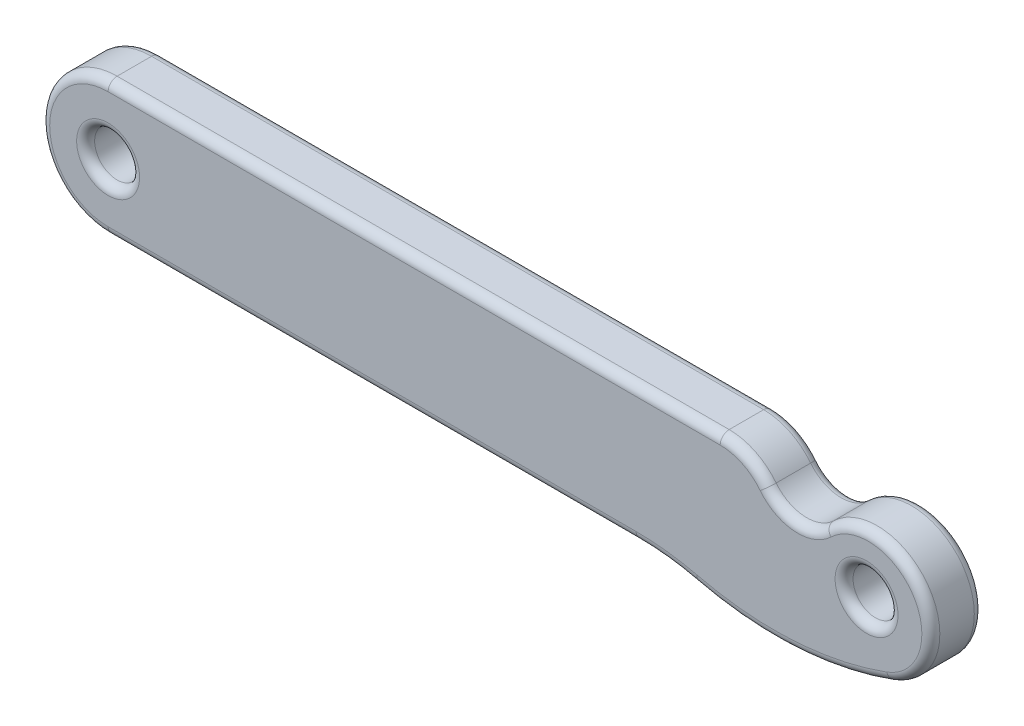
SolidWorks part; units mm, degrees
ref_plane "Front" through (0, 0, 0) normal (0, 0, 1) x (1, 0, 0)
ref_plane "Top" through (0, 0, 0) normal (0, 1, 0) x (1, 0, 0)
ref_plane "Right" through (0, 0, 0) normal (1, 0, 0) x (0, 0, -1)
sketch "Sketch1" plane through (0, 0, 0) normal (0, 0, 1) x (1, 0, 0)
  line L0 (0, 0) -> (25.3139, 0) construction
  line L1 (0, 2.25) -> (25.3139, 2.25)
  line L2 (0, -2.25) -> (25.3139, -2.25)
  circle A0 centre (0, 0) radius 0.75
  arc A1 (0, 2.25) -> (0, -2.25) centre (0, 0) ccw
  arc A2 (25.3139, -2.25) -> (25.3139, 2.25) centre (25.3139, 0) ccw
  circle A3 centre (25.3139, 0) radius 0.75
  point P3 (12.657, 0)
  dimension "D1" = 1.5
  dimension "D2" = 25.3139
  dimension "D3" = 1.5
extrude "Boss-Extrude1" add sketch "Sketch1" along normal blind 1.75
sketch "Sketch2" plane through (0, 0, 0) normal (0, 0, 1) x (1, 0, 0)
  circle A1 centre (23.0178, 2.2961) radius 1
  point P1 (20.5222, 2.2705)
sketch "Sketch3" plane through (0, 0, 1.75) normal (0, 0, 1) x (1, 0, 0)
  line L1 (20.4287, 2.25) -> (19.3427, 2.25)
  line L3 (25.3139, 2.25) -> (0, 2.25) construction
  line L6 (25.0484, -2.2343) -> (28.6572, -4.175)
  line L7 (28.6572, -4.175) -> (32.3716, 3.4229)
  line L8 (32.3716, 3.4229) -> (23.3874, 7.4223)
  line L9 (23.3874, 7.4223) -> (19.3427, 2.25)
  arc A2 (20.4287, 2.25) -> (21.9979, 1.4901) centre (20.4287, 0.25) cw
  arc A10 (25.0484, -2.2343) -> (26.0877, -2.1128) centre (25.3139, 0) ccw
  arc A11 (25.3139, -2.25) -> (25.3139, 2.25) centre (25.3139, 0) ccw construction
  arc A12 (21.9979, 1.4901) -> (23.9188, 1.359) centre (23.0178, 2.2961) ccw
  circle A13 centre (23.0178, 2.2961) radius 1 construction
  arc A14 (23.9188, 1.359) -> (26.0877, -2.1128) centre (25.3684, -0.1488) cw
  point P19 (21.7186, 2.25)
  point P20 (26.0877, -2.1128)
  dimension "D1" = 0.3
  dimension "D2" = 2
extrude "Cut-Extrude1" cut sketch "Sketch3" against normal through all
sketch "Sketch4" plane through (0, 0, 1.75) normal (0, 0, 1) x (1, 0, 0)
  line L8 (0, -2.25) -> (25.0776, -2.25) construction
  line L9 (17.6232, -2.25) -> (26.0877, -2.1128)
  arc A16 (26.0877, -2.1128) -> (19.5949, -2.4844) centre (22.2272, 8.4279) cw
  arc A17 (25.0484, -2.2343) -> (26.0877, -2.1128) centre (25.3139, 0) ccw construction
  arc A18 (17.6232, -2.25) -> (19.5949, -2.4844) centre (17.6232, -10.658) cw
  arc A19 (26.0877, -2.1128) -> (23.9188, 1.359) centre (25.3684, -0.1488) ccw construction
  point P10 (26.6539, -1.7987)
  point P14 (19.5949, -2.4844)
extrude "Boss-Extrude2" add sketch "Sketch4" against normal up to vertex (1.75 mm away) up to point (0, 2.25, 0)
fillet "Fillet1" radius 0.3 20 edges at (26.0639, 0, 0) (0.75, 0, 0) (8.8116, -2.25, 0) (10.2144, 2.25, 0) (-2.25, 0, 0) (26.0639, 0, 1.75) (0.75, 0, 1.75) (10.2144, 2.25, 1.75) (8.8116, -2.25, 1.75) (-2.25, 0, 1.75) (27.1423, 0.9594, 0) (22.9293, 0.9991, 0) (21.3005, 2.05, 0) (18.616, -2.3088, 1.75) (18.616, -2.3088, 0) (22.8688, -2.7791, 1.75) (22.8688, -2.7791, 0) (21.3005, 2.05, 1.75) (22.9293, 0.9991, 1.75) (27.1423, 0.9594, 1.75)
